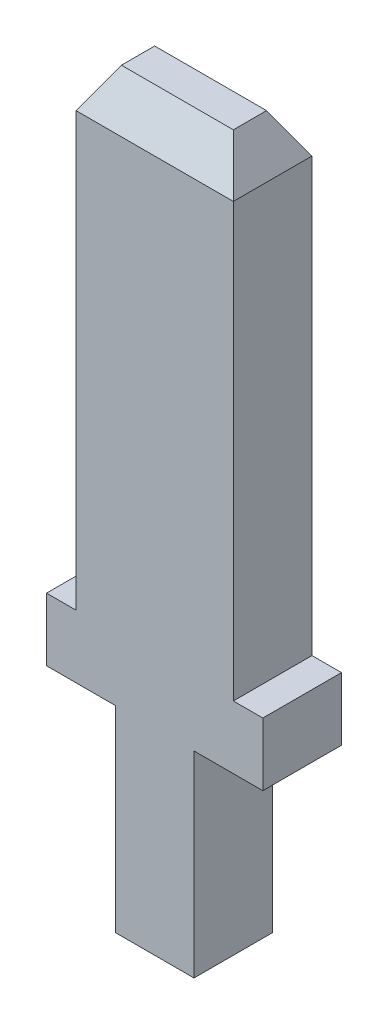
SolidWorks part; units mm, degrees
material "Медь"
ref_plane "Спереди" through (0, 0, 0) normal (0, 0, 1) x (1, 0, 0)
ref_plane "Сверху" through (0, 0, 0) normal (0, 1, 0) x (1, 0, 0)
ref_plane "Справа" through (0, 0, 0) normal (1, 0, 0) x (0, 0, -1)
sketch "Эскиз1" plane through (0, 0, 0) normal (0, 0, 1) x (1, 0, 0)
  line L0 (1, 0) -> (-1, 0)
  line L1 (-1, 0) -> (-1, 5)
  line L2 (-1, 5) -> (-2.75, 5)
  line L3 (-2.75, 5) -> (-2.75, 6.6)
  line L4 (-2.75, 6.6) -> (-2, 6.6)
  line L5 (-2, 6.6) -> (-2, 18.6)
  line L6 (-2, 18.6) -> (2, 18.6)
  line L7 (0, 18.6) -> (0, 0) construction
  line L8 (2, 6.6) -> (2, 18.6)
  line L9 (2.75, 6.6) -> (2, 6.6)
  line L10 (2.75, 5) -> (2.75, 6.6)
  line L11 (1, 5) -> (2.75, 5)
  line L12 (1, 0) -> (1, 5)
  dimension "D1" = 12
  dimension "D2" = 2
  dimension "D3" = 2.75
  dimension "D4" = 13.6
  dimension "D5" = 5
  dimension "D6" = 1
extrude "Бобышка-Вытянуть1" add sketch "Эскиз1" along normal mid plane 2
chamfer "Фаска1" distance 1 angle 30 4 edges at (2, 18.6, 0) (0, 18.6, 1) (-2, 18.6, 0) (0, 18.6, -1)
